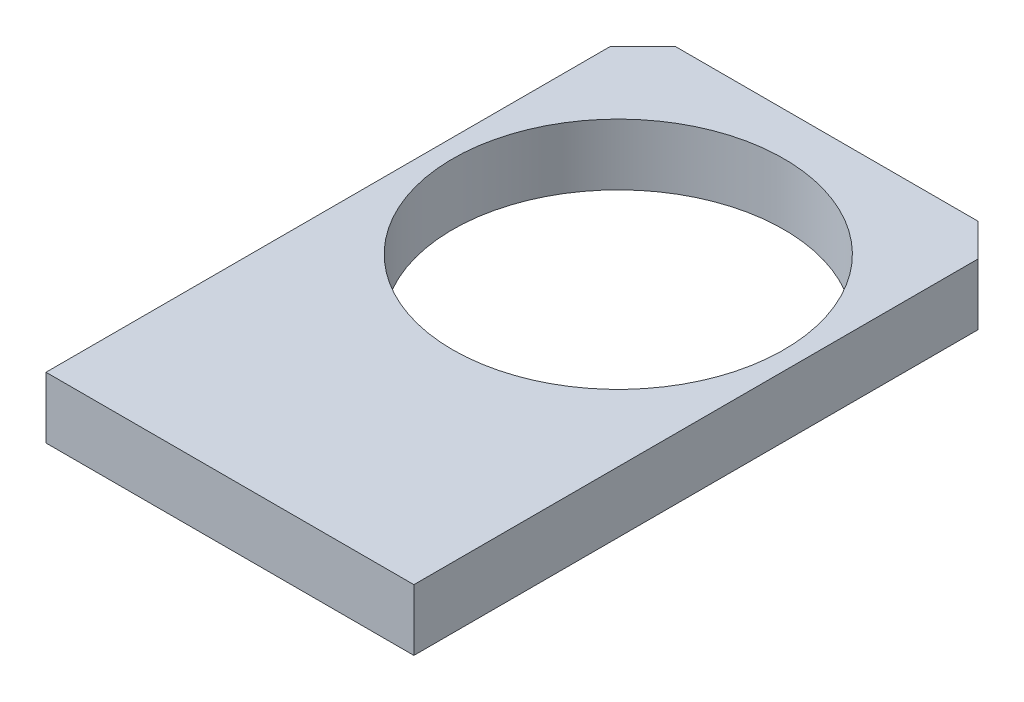
SolidWorks part; units mm, degrees
ref_plane "Front Plane" through (0, 0, 0) normal (0, 0, 1) x (1, 0, 0)
ref_plane "Top Plane" through (0, 0, 0) normal (0, 1, 0) x (1, 0, 0)
ref_plane "Right Plane" through (0, 0, 0) normal (1, 0, 0) x (0, 0, -1)
sketch "Sketch1" plane through (0, 0, 0) normal (0, 1, 0) x (1, 0, 0)
  line L1 (-22.5, 0) -> (22.5, 0)
  line L2 (-22.5, 0) -> (-22.5, 73)
  line L3 (-22.5, 73) -> (22.5, 73)
  line L4 (22.5, 0) -> (22.5, 73)
  circle A0 centre (0, 47.5) radius 20.25
  point P7 (0, 0)
  dimension "D3" = 47.5
  dimension "D4" = 40.5
  dimension "D1" = 45
  dimension "D2" = 73
extrude "Boss-Extrude1" add sketch "Sketch1" along normal blind 7.5
cosmetic thread "Cosmetic Thread1" parameters "D2"=41
chamfer "Chamfer1" distance 4 angle 45 2 edges at (-22.5, 3.75, -73) (22.5, 3.75, -73)
